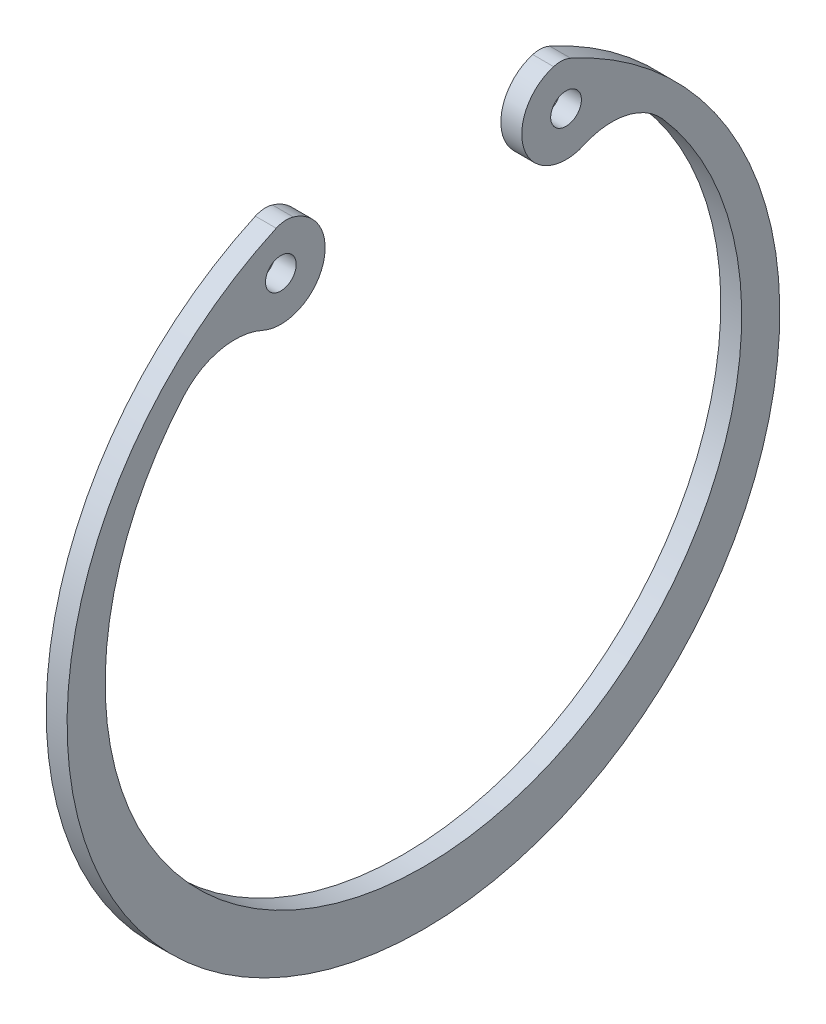
SolidWorks part; units mm, degrees
material "AISI Тип A2 Инструментальная сталь"
ref_plane "Спереди" through (0, 0, 0) normal (0, 0, 1) x (1, 0, 0)
ref_plane "Сверху" through (0, 0, 0) normal (0, 1, 0) x (1, 0, 0)
ref_plane "Справа" through (0, 0, 0) normal (1, 0, 0) x (0, 0, -1)
sketch "Эскиз1" plane through (0, 0, 0) normal (1, 0, 0) x (0, 0, -1)
  line L0 (0, -1000.3492) -> (0, 48999.6508) construction
  line L1 (10.5954, 26.5079) -> (13.0838, 19.7613) construction
  arc A10 (-11.9815, 26.4092) -> (11.9815, 26.4092) centre (0, 0) ccw
  circle A12 centre (11.6042, 23.0478) radius 1.25
  arc A13 (10.5954, 26.5079) -> (13.0838, 19.7613) centre (11.6042, 23.0478) ccw
  arc A14 (19.4778, 18.3712) -> (13.0838, 19.7613) centre (15.3416, 14.746) ccw
  circle A15 centre (-11.6042, 23.0478) radius 1.25
  arc A16 (-19.4778, 18.3712) -> (-13.0838, 19.7613) centre (-15.3416, 14.746) cw
  arc A17 (-10.5954, 26.5079) -> (-13.0838, 19.7613) centre (-11.6042, 23.0478) cw
  arc A18 (-10.5954, 26.5079) -> (-11.9815, 26.4092) centre (-11.1552, 24.5878) ccw
  arc A19 (-19.4778, 18.3712) -> (19.4778, 18.3712) centre (0, 1.3) ccw
  arc A20 (10.5954, 26.5079) -> (11.9815, 26.4092) centre (11.1552, 24.5878) cw
  point P21 (-11.44, 26.6482)
  point P25 (11.44, 26.6482)
  dimension "D1" = 58
  dimension "d4" = 2.5
  dimension "r1" = 5.5
  dimension "r2" = 2
  dimension "r2_2" = 2
  dimension "D2" = 25.9
  dimension "e" = 1.3
  dimension "a" = 6.8
  dimension "l" = 16
extrude "Бобышка-Вытянуть1" add sketch "Эскиз1" along normal blind 1.7
sketch "Эскиз канавки" plane through (0, 0, 0) normal (0, 0, 1) x (1, 0, 0)
  line L1 (1.7, -29) -> (-0.2, -29)
  line L2 (1.7, -29) -> (1.7, 0)
  line L3 (1.7, 0) -> (-0.2, 0)
  line L4 (-0.2, -29) -> (-0.2, 0)
  dimension "D1" = 1.9
sketch "при одностор ось нагр" plane through (0, 0, 0) normal (0, 0, 1) x (1, 0, 0)
  line L0 (1.7, -29) -> (6.2, -29)
  dimension "h" = 4.5
equation "\"r2_2@Эскиз1\"=\"r2@Эскиз1\""
equation "\"D2@Эскиз1\"=51.8/2"
